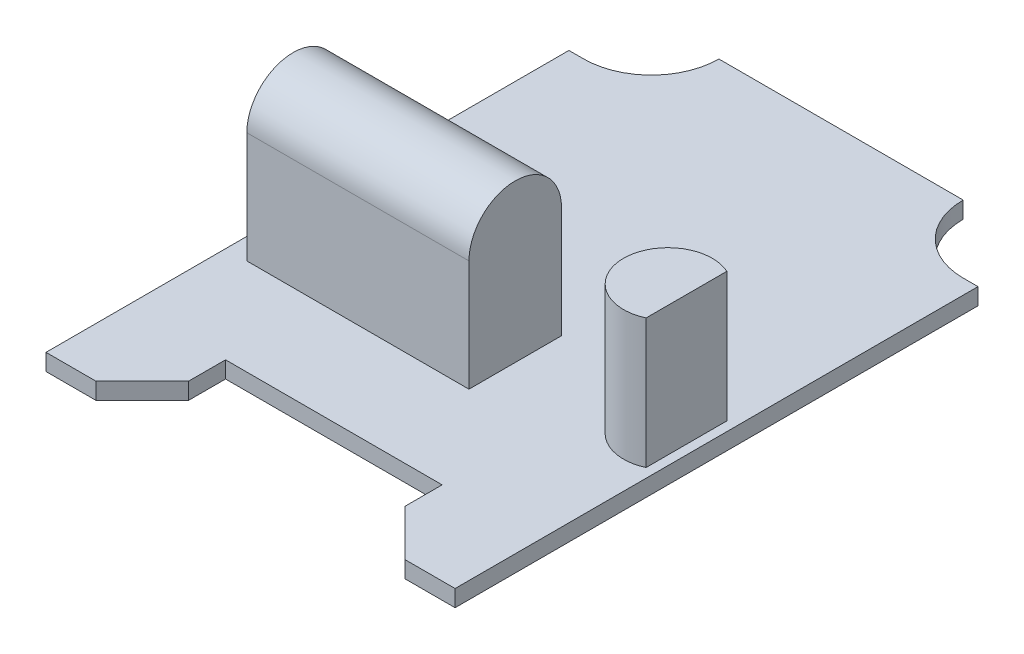
SolidWorks part; units mm, degrees
ref_plane "Front Plane" through (0, 0, 0) normal (0, 0, 1) x (1, 0, 0)
ref_plane "Top Plane" through (0, 0, 0) normal (0, 1, 0) x (1, 0, 0)
ref_plane "Right Plane" through (0, 0, 0) normal (1, 0, 0) x (0, 0, -1)
sketch "Sketch1" plane through (0, 0, 0) normal (0, 1, 0) x (1, 0, 0)
  line L0 (-11.05, 0) -> (-11.05, 28.25)
  line L1 (-11.05, 28.25) -> (-10.25, 28.25)
  line L2 (-6.6, 31.9) -> (6.6, 31.9)
  line L3 (0, 0) -> (0, 31.9) construction
  line L4 (-11.05, 0) -> (0, 0) construction
  line L5 (-6.6, 31.9) -> (-6.6, 34.2533) construction
  line L6 (-5.85, 4.5) -> (-5.85, 2.5)
  line L7 (-5.85, 2.5) -> (-8.35, 0)
  line L8 (-8.35, 0) -> (-11.05, 0)
  line L9 (-5.85, 4.5) -> (5.85, 4.5)
  line L10 (5.85, 4.5) -> (5.85, 2.5)
  line L11 (5.85, 2.5) -> (8.35, 0)
  line L12 (8.35, 0) -> (11.05, 0)
  line L13 (11.05, 0) -> (11.05, 28.25)
  line L14 (11.05, 28.25) -> (10.25, 28.25)
  arc A0 (-6.6, 31.9) -> (-10.25, 28.25) centre (-10.25, 31.9) cw
  arc A1 (6.6, 31.9) -> (10.25, 28.25) centre (10.25, 31.9) ccw
  point P14 (0, 4.5)
  dimension "D1" = 11.05
  dimension "D2" = 28.25
  dimension "D3" = 6.6
  dimension "D4" = 31.9
  dimension "D5" = 5.2
  dimension "D6" = 135
  dimension "D7" = 4.5
  dimension "D8" = 2.5
extrude "Boss-Extrude1" add sketch "Sketch1" along normal blind 0.9
sketch "Sketch2" plane through (0, 0.9, 0) normal (0, 1, 0) x (1, 0, 0)
  line L0 (0, 31.9) -> (0, 0) construction
  line L1 (6.6, 31.9) -> (-6.6, 31.9) construction
  line L2 (0, 9.2) -> (-9.9, 9.2)
  line L3 (-9.9, 9.2) -> (-9.9, 4.5)
  line L4 (-9.9, 4.5) -> (-1, 4.5)
  line L5 (-1, 4.5) -> (0, 5.5)
  line L6 (0, 5.5) -> (0, 9.2)
  line L7 (-5.85, 4.5) -> (5.85, 4.5) construction
  line L8 (-9.4, 8.7) -> (-9.4, 5)
  line L9 (-9.4, 5) -> (-1.2071, 5)
  line L10 (-1.2071, 5) -> (-0.5, 5.7071)
  line L11 (-0.5, 5.7071) -> (-0.5, 8.7)
  line L12 (-0.5, 8.7) -> (-9.4, 8.7)
  dimension "D1" = 135
  dimension "D2" = 9.9
  dimension "D3" = 4.7
  dimension "D4" = 1
  dimension "D5" = 0.5
extrude "Boss-Extrude2" [suppressed] add sketch "Sketch2" along normal blind 6
pattern_linear "LPattern1" [suppressed] count 2 spacing 9.9
sketch "Sketch3" plane through (0, 0, 0) normal (0, -1, 0) x (1, 0, 0)
  line L0 (10.55, -10.8183) -> (10.55, -15.1817)
  line L1 (11.05, 0) -> (11.05, -28.25) construction
  line L2 (8.35, 0) -> (11.05, 0) construction
  arc A0 (10.55, -10.8183) -> (10.55, -15.1817) centre (9.55, -13) ccw
  dimension "D3" = 2.4
  dimension "D1" = 0.5
  dimension "D2" = 1
  dimension "D4" = 13
extrude "Boss-Extrude3" [suppressed] add sketch "Sketch3" along normal blind 7
ref_plane "Plane1" through (-9.9, 0, 0) normal (-1, 0, 0) x (0, 0, 1)
sketch "Sketch4" plane through (-9.9, 0, 0) normal (-1, 0, 0) x (0, 0, 1)
  line L0 (-9.7, 0.9) -> (-9.7, 6.9)
  line L1 (-28.25, 0.9) -> (0, 0.9) construction
  line L2 (-14.7, 0.9) -> (-14.7, 6.9)
  line L3 (-12.2, 9.4) -> (-13.203, 9.4) construction
  line L5 (-14.7, 0.9) -> (-9.7, 0.9)
  arc A0 (-14.7, 6.9) -> (-9.7, 6.9) centre (-12.2, 6.9) cw
  dimension "D2" = 2.5
  dimension "D1" = 8.5
  dimension "D3" = 9.7
extrude "Boss-Extrude4" add sketch "Sketch4" against normal blind 12
sketch "Sketch5" plane through (0, 0.9, 0) normal (0, 1, 0) x (1, 0, 0)
  line L0 (10.55, 15.1817) -> (10.55, 10.8183)
  line L1 (8.35, 0) -> (11.05, 0) construction
  line L2 (11.05, 0) -> (11.05, 28.25) construction
  arc A0 (10.55, 15.1817) -> (10.55, 10.8183) centre (9.55, 13) ccw
  dimension "D2" = 2.4
  dimension "D1" = 13
  dimension "D3" = 1
  dimension "D4" = 0.5
extrude "Boss-Extrude5" add sketch "Sketch5" along normal blind 7
